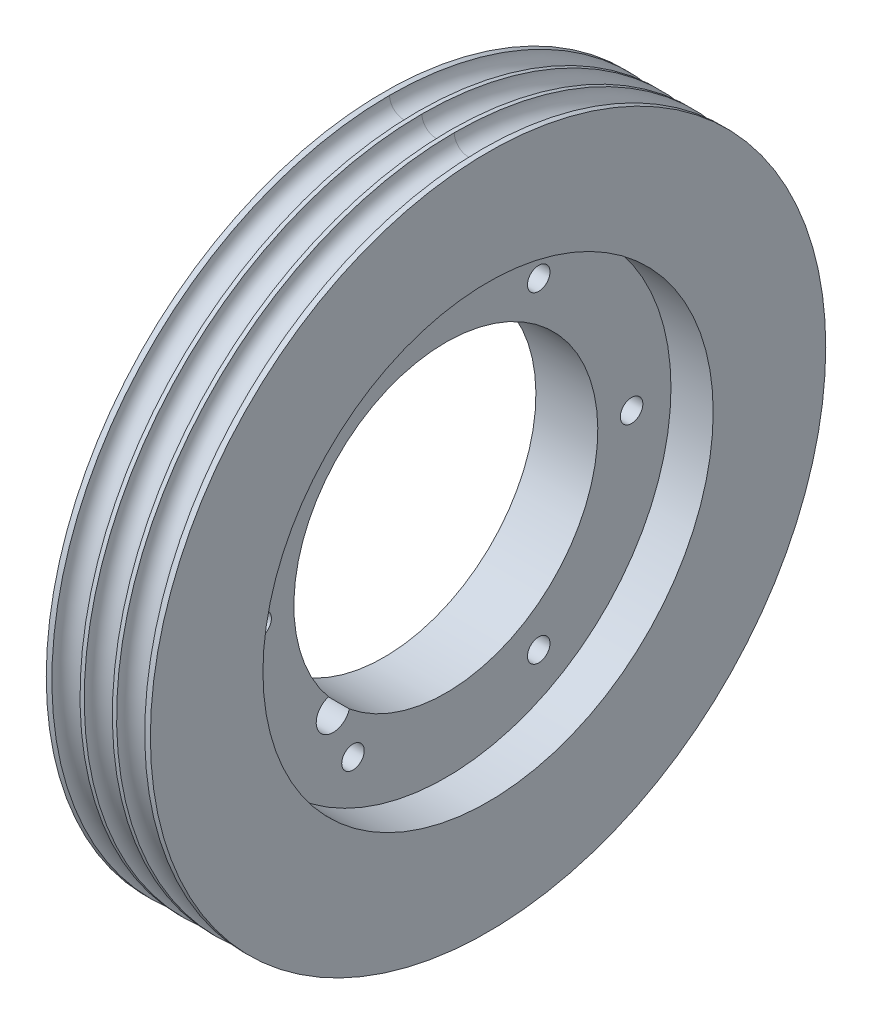
SolidWorks part; units mm, degrees
ref_plane "Front Plane" through (0, 0, 0) normal (0, 0, 1) x (1, 0, 0)
ref_plane "Top Plane" through (0, 0, 0) normal (0, 1, 0) x (1, 0, 0)
ref_plane "Right Plane" through (0, 0, 0) normal (1, 0, 0) x (0, 0, -1)
sketch "Sketch1" plane through (0, 0, 0) normal (1, 0, 0) x (0, 0, -1)
  circle A0 centre (0, 0) radius 60
extrude "Boss-Extrude1" add sketch "Sketch1" along normal mid plane 18.5
sketch "Sketch3" plane through (-9.25, 0, 0) normal (-1, 0, 0) x (0, 0, 1)
  circle A0 centre (0, 0) radius 27
extrude "Cut-Extrude1" cut sketch "Sketch3" against normal blind 15
sketch "Sketch4" plane through (-9.25, 0, 0) normal (-1, 0, 0) x (0, 0, 1)
  circle A0 centre (33, 0) radius 2
  dimension "D1" = 33
extrude "Cut-Extrude2" cut sketch "Sketch4" against normal blind 15
sketch "Sketch5" plane through (-9.25, 0, 0) normal (-1, 0, 0) x (0, 0, 1)
  circle A0 centre (33, 0) radius 4
extrude "Cut-Extrude3" cut sketch "Sketch5" against normal blind 3
pattern_circular "CirPattern1" count 6 over 360 about axis through (0, 0, 0) along (1, 0, 0) of "Cut-Extrude3", "Cut-Extrude2"
sketch "Sketch6" plane through (-9.25, 0, 0) normal (-1, 0, 0) x (0, 0, 1)
  line L0 (0, 0) -> (25.5888, 0) construction
  line L1 (20.0323, -20.0323) -> (0, 0) construction
  circle A0 centre (20.0323, -20.0323) radius 3
  dimension "D1" = 28.33
  dimension "D2" = 45
extrude "Cut-Extrude4" cut sketch "Sketch6" against normal up to next
sketch "Sketch7" plane through (0, 0, 0) normal (0, 0, 1) x (1, 0, 0)
  line L0 (0, 0) -> (0, 60.3044) construction
  line L1 (9.25, -60) -> (9.25, 60) construction
  circle A0 centre (5.75, 60.0071) radius 2.5
  circle A1 centre (-5.75, 60.0071) radius 2.5
  circle A2 centre (0, 60.0071) radius 2.5
  dimension "D1" = 3.5
sweep "Cut-Sweep1" cut profiles "Sketch7" path edge at (-9.25, 0, -60)
sketch "Sketch8" plane through (9.25, 0, 0) normal (1, 0, 0) x (0, 0, -1)
  circle A0 centre (0, 0) radius 40
extrude "Cut-Extrude5" cut sketch "Sketch8" against normal blind 7.5
